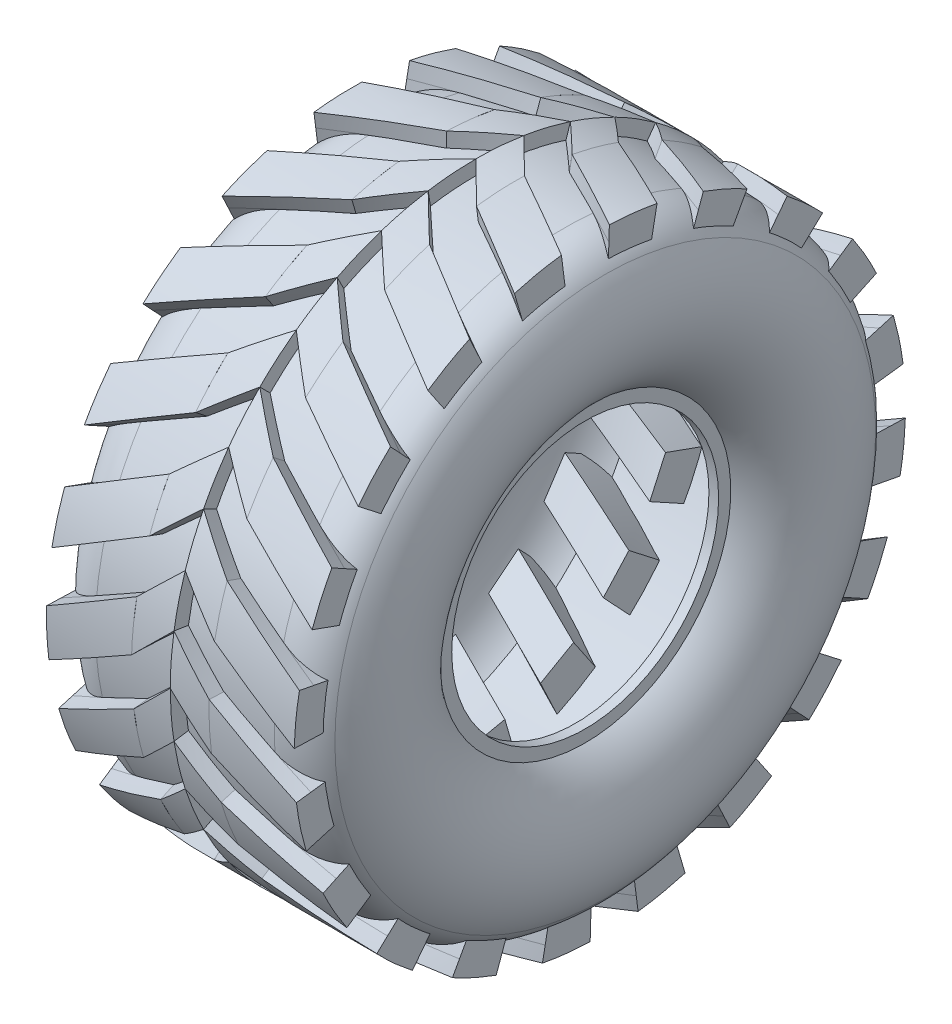
SolidWorks part; units mm, degrees
ref_plane "Alzado" through (0, 0, 0) normal (0, 0, 1) x (1, 0, 0)
ref_plane "Planta" through (0, 0, 0) normal (0, 1, 0) x (1, 0, 0)
ref_plane "Vista lateral" through (0, 0, 0) normal (1, 0, 0) x (0, 0, -1)
sketch "Croquis2" plane through (0, 0, 0) normal (0, 0, 1) x (1, 0, 0)
  line L0 (0, 0) -> (0, 27.5) construction
  line L1 (0, 27.5) -> (22.5, 27.5) construction
  line L2 (22.5, 27.5) -> (22.5, 30)
  line L3 (22.5, 30) -> (11.25, 45) construction
  line L4 (11.25, 45) -> (22.5, 60) construction
  line L5 (11.25, 45) -> (30, 45) construction
  line L6 (22.5, 60) -> (0, 60)
  line L7 (22.5, 27.5) -> (20.5, 27.5)
  line L8 (20.5, 29.5) -> (20.5, 29.5)
  line L9 (20.5, 29.5) -> (20.5, 31.0358)
  line L10 (21.8123, 58) -> (0, 58)
  line L11 (20.5, 29.5) -> (20.5, 27.5)
  line L12 (20.5, 27.5) -> (20.5, 29.5)
  line L13 (-22.5, 27.5) -> (-20.5, 27.5)
  line L14 (-22.5, 27.5) -> (-22.5, 30)
  line L15 (-20.5, 29.5) -> (-20.5, 31.0358)
  line L16 (-20.5, 29.5) -> (-20.5, 27.5)
  line L17 (-21.8123, 58) -> (0, 58)
  line L18 (-22.5, 60) -> (0, 60)
  line L19 (0, 0) -> (22.5, 0) construction
  line L20 (22.5, 0) -> (22.5, 27.5) construction
  arc A0 (22.5, 30) -> (22.5, 60) centre (11.25, 45) ccw
  arc A1 (20.5, 31.0358) -> (21.8123, 58) centre (11.25, 45) ccw
  arc A2 (-22.5, 30) -> (-22.5, 60) centre (-11.25, 45) cw
  arc A3 (-20.5, 31.0358) -> (-21.8123, 58) centre (-11.25, 45) cw
  dimension "D1" = 2.5
  dimension "D2" = 22.5
  dimension "D3" = 30
  dimension "D4" = 30
  dimension "D5" = 60
  dimension "D6" = 2
  dimension "D7" = 2
revolve "Revolución1" add sketch "Croquis2" angle 360 about L19
fillet "Redondeo1" radius 10 2 edges at (-22.5, 0, 60) (22.5, 0, 60)
sketch "Croquis3" plane through (0, 0, 0) normal (1, 0, 0) x (0, 0, -1)
  line L0 (0, 0) -> (0, 60) construction
  line L1 (0, 60) -> (0, 63) construction
  line L2 (-9.8554, 62.2244) -> (-9.3861, 59.2613) construction
  line L3 (-9.8554, 62.2244) -> (-9.3861, 59.2613)
  line L4 (0, 63) -> (0, 60)
  circle A0 centre (0, 0) radius 60 construction
  circle A1 centre (0, 0) radius 60 construction
  arc A2 (0, 63) -> (-9.8554, 62.2244) centre (0, 0) ccw
  arc A3 (0, 60) -> (-9.3861, 59.2613) centre (0, 0) ccw
  dimension "D1" = 3
  dimension "D2" = 9
sketch "Croquis5" plane through (0, 0, 0) normal (1, 0, 0) x (0, 0, -1)
  circle A0 centre (0, 0) radius 60 construction
  circle A1 centre (0, 0) radius 60
curve "Hélice/Espiral1" pitch 400 height 8 turns 0.02
sketch "Croquis6" plane through (0, 0, 0) normal (1, 0, 0) x (0, 0, -1)
  line L0 (0, 63) -> (0, 60) construction
  line L1 (-9.8554, 62.2244) -> (-9.3861, 59.2613) construction
  line L2 (0, 63) -> (0, 60)
  line L3 (-9.8554, 62.2244) -> (-9.3861, 59.2613)
  arc A0 (0, 60) -> (-9.3861, 59.2613) centre (0, 0) ccw construction
  arc A1 (0, 63) -> (-9.8554, 62.2244) centre (0, 0) ccw construction
  arc A2 (0, 60) -> (-9.3861, 59.2613) centre (0, 0) ccw
  arc A3 (0, 63) -> (-9.8554, 62.2244) centre (0, 0) ccw
sweep "Barrer1" add profiles "Croquis6" path "Hélice/Espiral1"
sketch "Croquis7" plane through (-7.9997, 0, 0) normal (-1, 0, 0) x (0, 0, 1)
  line L0 (16.7397, 57.6176) -> (13.9498, 48.0146)
  line L1 (13.9498, 48.0146) -> (6.2669, 49.6057)
  line L2 (7.8963, 62.5032) -> (7.5202, 59.5268)
  line L3 (16.7397, 57.6176) -> (17.5767, 60.4984)
  line L4 (7.8963, 62.5032) -> (7.5202, 59.5268)
  line L5 (16.7397, 57.6176) -> (17.5767, 60.4984)
  line L6 (6.2669, 49.6057) -> (7.5202, 59.5268)
  parabola Q2 (17.5767, 60.4984) -> (7.8963, 62.5032) focus (6.4064, 30.9346) apex (12.7759, 61.6912)
  parabola Q3 (17.5767, 60.4984) -> (7.8963, 62.5032) focus (6.4064, 30.9346) apex (12.7759, 61.6912)
  parabola Q4 (7.5202, 59.5268) -> (16.7397, 57.6176) focus (6.1019, 29.4644) apex (12.1675, 58.7536)
  parabola Q5 (7.5202, 59.5268) -> (16.7397, 57.6176) focus (6.1019, 29.4644) apex (12.1675, 58.7536) construction
  dimension "D2" = 10
  dimension "D1" = 0
sketch "Croquis8" plane through (-7.9997, 0, 0) normal (-1, 0, 0) x (0, 0, 1)
  circle A0 centre (0, 0) radius 60 construction
  circle A1 centre (0, 0) radius 60
curve "Hélice/Espiral2" pitch 700 height 17.5 turns 0.025
sweep "Barrer2" add profiles "Croquis7" path "Hélice/Espiral2"
mirror "Simetría3" about plane through (0, 0, 0) normal (1, 0, 0) of bodies 102 103
ref_axis "Eje1" through (246.142, 0, 0) along (-1, 0, 0)
pattern_circular "MatrizC2" count 2 every 9 about axis through (246.142, 0, 0) along (-1, 0, 0) of bodies 106 107
delete or keep bodies "Sólido-Eliminar1" type delete bodies bodies 106
delete or keep bodies "Sólido-Eliminar2" type delete bodies bodies 107
pattern_circular "MatrizC3" count 20 over 360 about axis through (246.142, 0, 0) along (-1, 0, 0)
